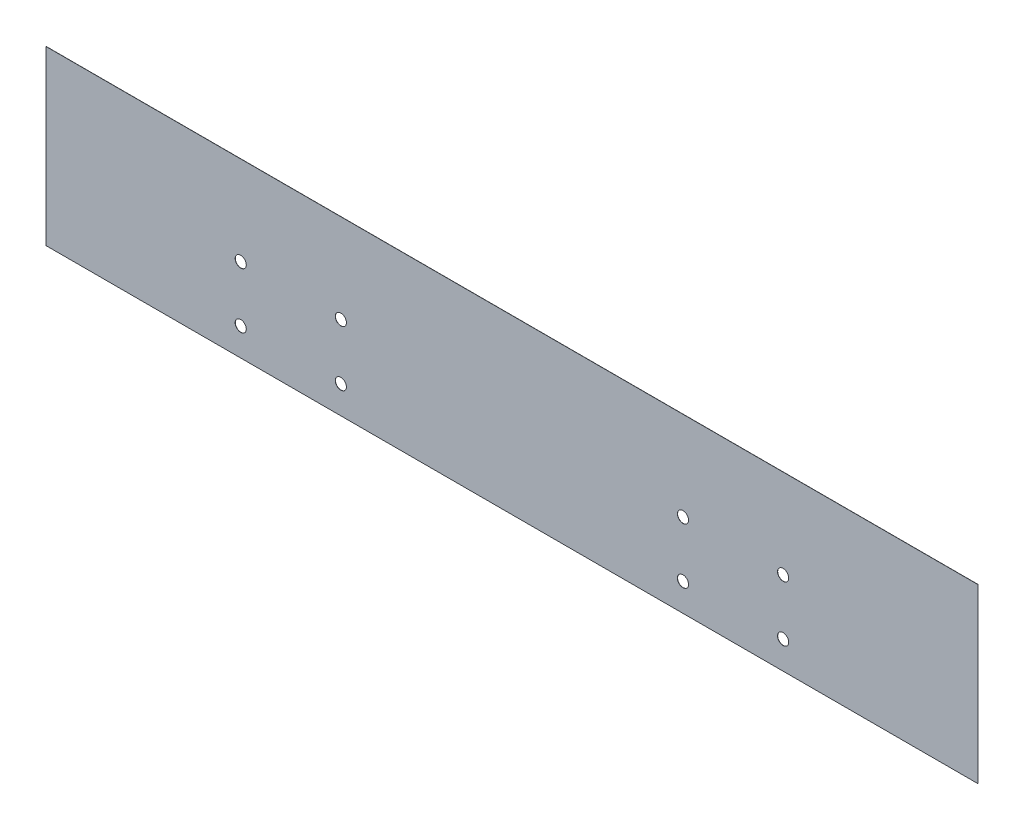
SolidWorks part; units mm, degrees
ref_plane "Front Plane" through (0, 0, 0) normal (0, 0, 1) x (1, 0, 0)
ref_plane "Top Plane" through (0, 0, 0) normal (0, 1, 0) x (1, 0, 0)
ref_plane "Right Plane" through (0, 0, 0) normal (1, 0, 0) x (0, 0, -1)
sketch "Sketch1" plane through (0, 0, 0) normal (0, 0, 1) x (1, 0, 0)
  line L1 (-167.5, -31) -> (167.5, -31)
  line L2 (-167.5, -31) -> (-167.5, 31)
  line L3 (-167.5, 31) -> (167.5, 31)
  line L4 (167.5, -31) -> (167.5, 31)
  line L5 (-167.5, -31) -> (167.5, 31) construction
  line L6 (-167.5, 31) -> (167.5, -31) construction
  point P0 (0, 0)
  dimension "D1" = 335
  dimension "D2" = 62
extrude "Body" add sketch "Sketch1" along normal blind 0.0625
sketch "Sketch2" plane through (0, 0, 0.0625) normal (0, 0, 1) x (1, 0, 0)
  line L0 (-61.5, -1) -> (61.5, -1) construction
  line L1 (61.5, -1) -> (61.5, -21) construction
  line L2 (61.5, -21) -> (-61.5, -21) construction
  line L3 (-61.5, -21) -> (-61.5, -1) construction
  line L4 (0, -1) -> (0, -21) construction
  line L5 (-167.5, -31) -> (167.5, -31) construction
  circle A0 centre (-61.5, -1) radius 2
  circle A1 centre (-61.5, -21) radius 2
  circle A2 centre (61.5, -1) radius 2
  circle A3 centre (61.5, -21) radius 2
  point P10 (-1.1786, -15.4224)
  dimension "D4" = 4
  dimension "D1" = 123
  dimension "D2" = 20
  dimension "D3" = 10
extrude "Camera Mounting holes" cut sketch "Sketch2" against normal blind 0.0625
sketch "Sketch3" plane through (0, 0, 0.0625) normal (0, 0, 1) x (1, 0, 0)
  line L0 (-97.5, -1) -> (97.5, -1) construction
  line L1 (-97.5, -21) -> (97.5, -21) construction
  line L2 (-97.5, -1) -> (-97.5, -21) construction
  line L3 (97.5, -1) -> (97.5, -21) construction
  line L4 (-167.5, -31) -> (167.5, -31) construction
  line L5 (-167.5, 31) -> (-167.5, -31) construction
  line L6 (167.5, -31) -> (167.5, 31) construction
  circle A0 centre (-97.5, -1) radius 2
  circle A1 centre (-97.5, -21) radius 2
  circle A2 centre (97.5, -1) radius 2
  circle A3 centre (97.5, -21) radius 2
  dimension "D1" = 4
  dimension "D2" = 10
  dimension "D3" = 20
  dimension "D4" = 70
  dimension "D5" = 70
extrude "Mounting Holes" cut sketch "Sketch3" against normal blind 0.0625
